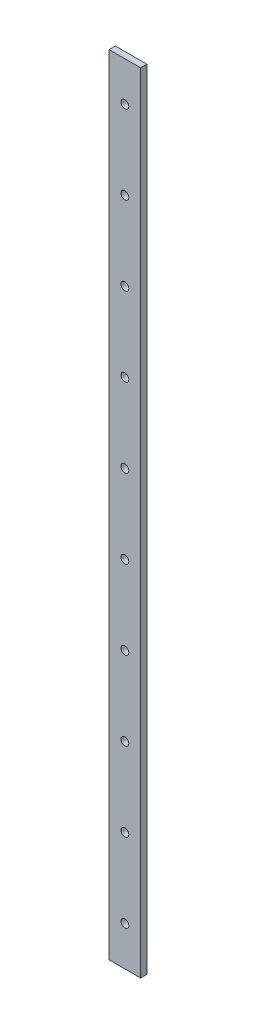
SolidWorks part; units mm, degrees
ref_plane "Спереди" through (0, 0, 0) normal (0, 0, 1) x (1, 0, 0)
ref_plane "Сверху" through (0, 0, 0) normal (0, 1, 0) x (1, 0, 0)
ref_plane "Справа" through (0, 0, 0) normal (1, 0, 0) x (0, 0, -1)
sketch "Эскиз1" plane through (0, 0, 0) normal (0, 1, 0) x (1, 0, 0)
  line L1 (-10, 2) -> (10, 2)
  line L2 (-10, 2) -> (-10, -2)
  line L3 (-10, -2) -> (10, -2)
  line L4 (10, 2) -> (10, -2)
  line L5 (-10, 2) -> (10, -2) construction
  line L6 (-10, -2) -> (10, 2) construction
  point P0 (0, 0)
extrude "Бобышка-Вытянуть1" add sketch "Эскиз1" along normal blind 500
sketch "Эскиз2" plane through (0, 0, 2) normal (0, 0, 1) x (1, 0, 0)
  circle A0 centre (0, 25) radius 2.5
  circle A1 centre (0, 75) radius 2.5
  circle A2 centre (0, 125) radius 2.5
  circle A3 centre (0, 175) radius 2.5
  circle A4 centre (0, 225) radius 2.5
  circle A5 centre (0, 275) radius 2.5
  circle A6 centre (0, 325) radius 2.5
  circle A7 centre (0, 375) radius 2.5
  circle A8 centre (0, 425) radius 2.5
  circle A9 centre (0, 475) radius 2.5
  dimension "D1" = 10
extrude "Вырез-Вытянуть1" cut sketch "Эскиз2" against normal through all
